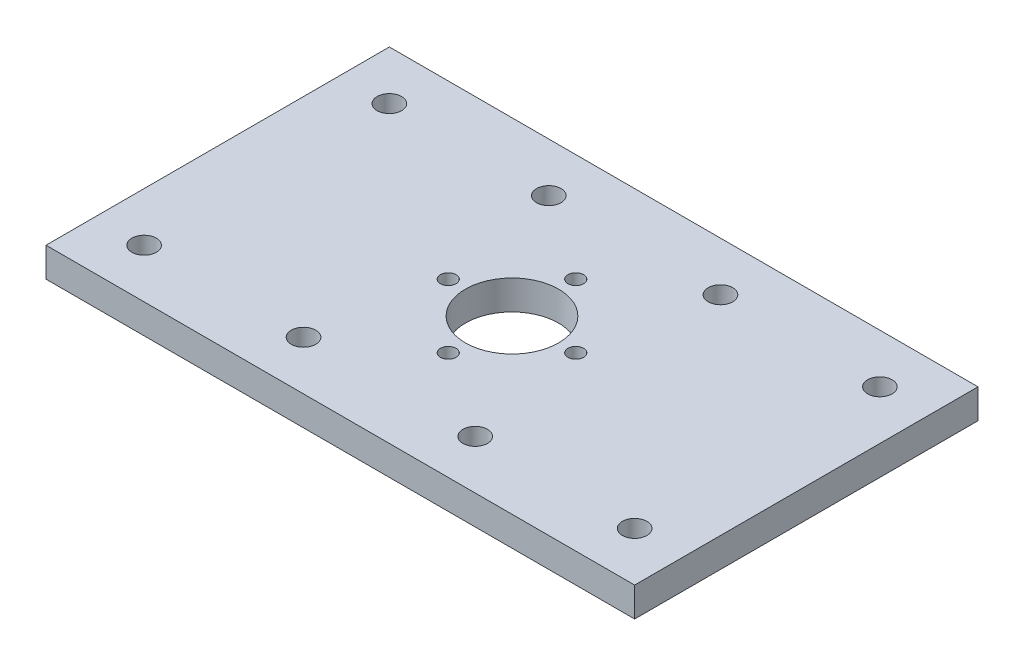
SolidWorks part; units mm, degrees
ref_plane "Front Plane" through (0, 0, 0) normal (0, 0, 1) x (1, 0, 0)
ref_plane "Top Plane" through (0, 0, 0) normal (0, 1, 0) x (1, 0, 0)
ref_plane "Right Plane" through (0, 0, 0) normal (1, 0, 0) x (0, 0, -1)
sketch "Sketch1" plane through (0, 0, 0) normal (0, 1, 0) x (1, 0, 0)
  line L0 (0, -3.3) -> (0, 3.3) construction
  line L1 (-60, 35) -> (60, 35)
  line L2 (-60, 35) -> (-60, -35)
  line L3 (-60, -35) -> (60, -35)
  line L4 (60, 35) -> (60, -35)
  line L5 (-60, 35) -> (60, -35) construction
  line L6 (-60, -35) -> (60, 35) construction
  line L7 (-3.3, 0) -> (3.3, 0) construction
  circle A0 centre (0, 0) radius 13 construction
  circle A1 centre (0, 13) radius 1.5 construction
  circle A2 centre (13, 0) radius 1.5 construction
  circle A3 centre (0, -13) radius 1.5 construction
  circle A4 centre (-13, 0) radius 1.5 construction
  circle A7 centre (0, 0) radius 9.5
  circle A8 centre (-17.5, 25) radius 2.5
  circle A9 centre (17.5, 25) radius 2.5
  circle A10 centre (17.5, -25) radius 2.5
  circle A11 centre (-17.5, -25) radius 2.5
  circle A12 centre (-50, 25) radius 2.5
  circle A13 centre (-50, -25) radius 2.5
  circle A14 centre (50, -25) radius 2.5
  circle A15 centre (50, 25) radius 2.5
  dimension "D1" = 26
  dimension "D2" = 3
  dimension "D4" = 19
  dimension "D7" = 5
  dimension "D10" = 5
  dimension "D5" = 17.5
  dimension "D6" = 120
  dimension "D8" = 70
  dimension "D9" = 25
  dimension "D11" = 50
  dimension "D12" = 25
  dimension "D3" = 4
extrude "Boss-Extrude1" add sketch "Sketch1" along normal blind 6
hole_wizard "CSK for M3 Flat Head Machine Screw1" positions "Sketch7" profile "Sketch8" countersink size "M3" standard "ANSI Metric" end condition through all
sketch "Sketch7" plane through (0, 0, 0) normal (0, -1, 0) x (-1, 0, 0)
  point P0 (-13, 0)
  point P3 (0, -13)
  point P6 (13, 0)
  point P9 (0, 13)
sketch "Sketch8" plane through (13, 0, 0) normal (1, 0, 0) x (0, 0, -1)
  line L0 (0, 0) -> (0, 6)
  line L1 (0, 6) -> (1.6, 6)
  line L2 (1.6, 6) -> (1.6, 1.55)
  line L3 (1.6, 1.55) -> (3.15, 0)
  line L5 (3.15, 0) -> (0, 0)
  line L6 (-1.6, 1.55) -> (-3.15, 0) construction
  line L11 (0, -6.35) -> (0, 107.95) construction
  dimension "Thru Hole Dia." = 3.2
  dimension "Thru Hole Depth" = 6
  dimension "Near C'Sink Dia." = 6.3
  dimension "Near C'Sink Angle" = 90
sketch "Sketch9" plane through (0, 0, 0) normal (0, 1, 0) x (1, 0, 0)
  line L0 (0, -3.3) -> (0, 3.3) construction
  line L1 (-3.3, 0) -> (3.3, 0) construction
  circle A0 centre (17.5, 25) radius 6
  circle A1 centre (-17.5, 25) radius 6
  circle A2 centre (-17.5, -25) radius 6
  circle A3 centre (17.5, -25) radius 6
  dimension "D1" = 12
equation "\"testbed_height\" = 91.50mm"
equation "\"plate_thickness\" = 6mm"
equation "\"main_body_splay_length\" = 48.5mm"
equation "\"splay_shaft_length_no_wires\" = 10mm"
equation "\"splay_shaft_length_wires\" = 6.5mm"
equation "\"timing_pulley_offset\" = 0mm"
equation "\"effective_motor_length\" = \"timing_pulley_offset\" + \"splay_shaft_length_no_wires\" + \"main_body_splay_length\""
equation "\"80_20_side\" = 25.4mm"
equation "\"80_20_length\" = 152.4mm"
equation "\"80_20_optic_mount_length\" = \"80_20_length\" - 25.4mm"
equation "\"optic_board_hole_size\" = 6.35mm"
equation "\"total_mounting_length\" = \"testbed_height\" - \"effective_motor_length\" - \"80_20_side\""
equation "\"mounting_vertical_portion_height\" = \"total_mounting_length\" - 2 * \"plate_thickness\""
equation "\"face_mount_width\" = 15.25mm"
equation "\"center_dist_to_face_mount_vertical_screws\" = 5mm"
equation "\"D1@Boss-Extrude1\"=\"plate_thickness\""
